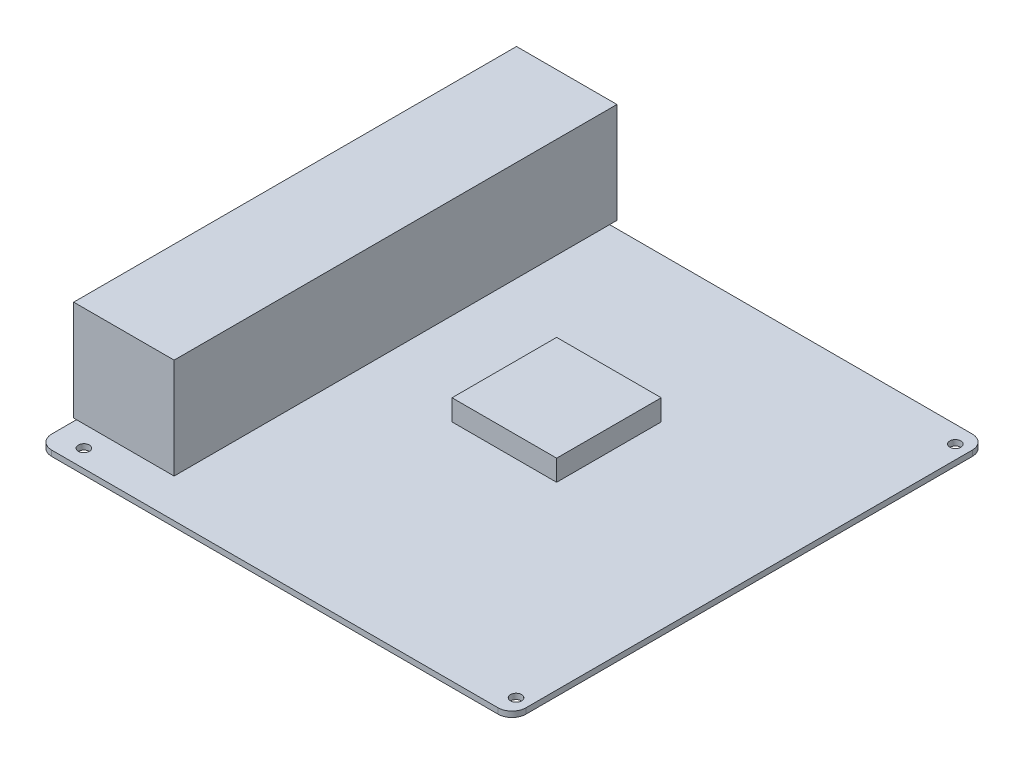
SolidWorks part; units mm, degrees
material "6061 합금"
ref_plane "정면" through (0, 0, 0) normal (0, 0, 1) x (1, 0, 0)
ref_plane "윗면" through (0, 0, 0) normal (0, 1, 0) x (1, 0, 0)
ref_plane "우측면" through (0, 0, 0) normal (1, 0, 0) x (0, 0, -1)
sketch "스케치1" plane through (0, 0, 0) normal (0, 1, 0) x (1, 0, 0)
  line L1 (-85, -85) -> (85, -85)
  line L2 (-85, -85) -> (-85, 85)
  line L3 (-85, 85) -> (85, 85)
  line L4 (85, -85) -> (85, 85)
  line L5 (-85, -85) -> (85, 85) construction
  line L6 (-85, 85) -> (85, -85) construction
  point P0 (0, 0)
  dimension "D1" = 170
extrude "보스-돌출1" add sketch "스케치1" along normal blind 2
sketch "스케치2" plane through (0, 2, 0) normal (0, 1, 0) x (1, 0, 0)
  line L0 (-85, 85) -> (-85, -85) construction
  line L1 (-85, -85) -> (85, -85) construction
  circle A0 centre (-74.84, -78.65) radius 1.98
  circle A1 centre (-51.98, 78.83) radius 1.98
  circle A2 centre (80.1, 78.83) radius 1.98
  circle A3 centre (80.1, -78.65) radius 1.98
  dimension "D1" = 3.96
  dimension "D2" = 22.86
  dimension "D3" = 10.16
  dimension "D4" = 157.48
  dimension "D5" = 6.35
  dimension "D6" = 154.94
extrude "컷-돌출1" cut sketch "스케치2" against normal through all
fillet "필렛1" radius 5 4 edges at (-85, 1, 85) (85, 1, 85) (85, 1, -85) (-85, 1, -85)
sketch "스케치3" plane through (0, 2, 0) normal (0, 1, 0) x (1, 0, 0)
  line L0 (-85, 80) -> (-85, -80) construction
  line L1 (-86, 87.62) -> (-50, 87.62)
  line L2 (-86, 87.62) -> (-86, -71.13)
  line L3 (-86, -71.13) -> (-50, -71.13)
  line L4 (-50, 87.62) -> (-50, -71.13)
  dimension "D1" = 7.52
  dimension "D2" = 158.75
  dimension "D3" = 1
  dimension "D4" = 36
surface "곡면-돌출1" sketch "스케치3" parameters "D1"=36
surface "곡면 채우기1"
surface "곡면 채우기2"
sketch "스케치4" plane through (0, 2, 0) normal (0, 1, 0) x (1, 0, 0)
  line L1 (-17, 33) -> (20.5, 33)
  line L2 (-17, 33) -> (-17, -4.5)
  line L3 (-17, -4.5) -> (20.5, -4.5)
  line L4 (20.5, 33) -> (20.5, -4.5)
  line L5 (-17, 33) -> (20.5, -4.5) construction
  line L6 (-17, -4.5) -> (20.5, 33) construction
  line L7 (85, -80) -> (85, 80) construction
  line L8 (80, 85) -> (-80, 85) construction
  point P0 (1.75, 14.25)
  dimension "D1" = 37.5
  dimension "D2" = 102
  dimension "D3" = 52
extrude "보스-돌출2" add sketch "스케치4" along normal blind 7.5 separate body
equation "\"Mass\"= \"SW-질량\" / 1000"
